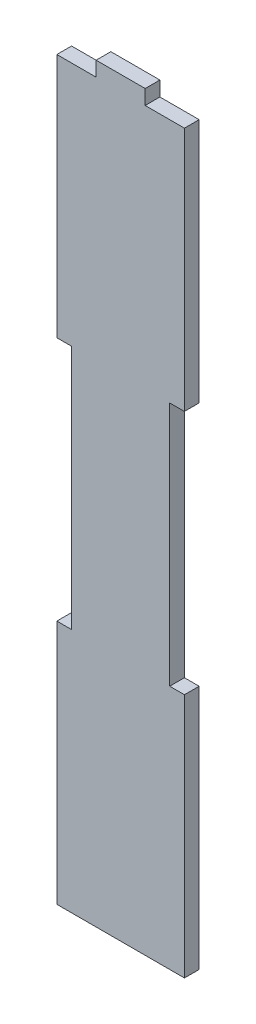
SolidWorks part; units mm, degrees
ref_plane "Front Plane" through (0, 0, 0) normal (0, 0, 1) x (1, 0, 0)
ref_plane "Top Plane" through (0, 0, 0) normal (0, 1, 0) x (1, 0, 0)
ref_plane "Right Plane" through (0, 0, 0) normal (1, 0, 0) x (0, 0, -1)
sketch "Sketch1" plane through (0, 0, 0) normal (0, 0, 1) x (1, 0, 0)
  line L0 (0, 100) -> (0, 150)
  line L1 (0, 0) -> (26, 0)
  line L2 (0, 0) -> (0, 50)
  line L3 (0, 150) -> (8, 150)
  line L4 (26, 0) -> (26, 50)
  line L5 (0, 100) -> (3, 100)
  line L7 (0, 50) -> (3, 50)
  line L8 (3, 100) -> (3, 50)
  line L9 (26, 100) -> (23, 100)
  line L11 (26, 50) -> (23, 50)
  line L12 (23, 100) -> (23, 50)
  line L14 (8, 150) -> (8, 153)
  line L15 (8, 153) -> (18, 153)
  line L16 (18, 150) -> (18, 153)
  line L17 (26, 100) -> (26, 150)
  line L18 (18, 150) -> (26, 150)
  point P17 (17.6144, 103)
  dimension "D1" = 150
  dimension "D2" = 20
  dimension "D3" = 3
  dimension "D4" = 50
  dimension "D5" = 10
extrude "Boss-Extrude1" add sketch "Sketch1" along normal blind 3
